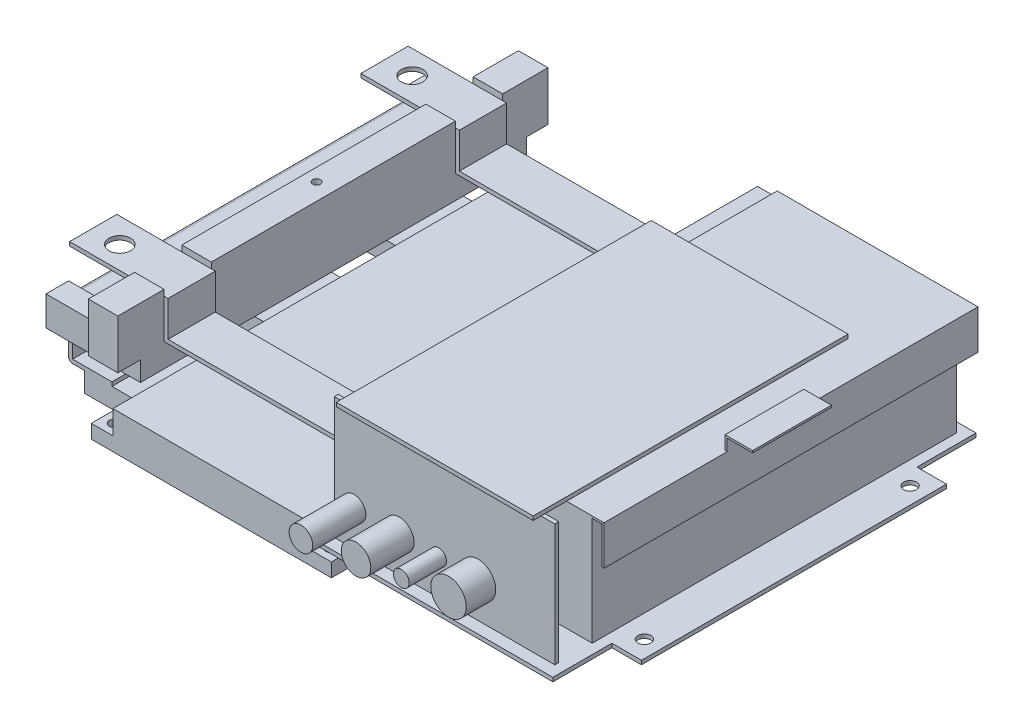
SolidWorks part; units mm, degrees
ref_plane "Płaszczyzna przednia" through (0, 0, 0) normal (0, 0, 1) x (1, 0, 0)
ref_plane "Płaszczyzna górna" through (0, 0, 0) normal (0, 1, 0) x (1, 0, 0)
ref_plane "Płaszczyzna prawa" through (0, 0, 0) normal (1, 0, 0) x (0, 0, -1)
sketch "Szkic1" plane through (0, 0, 0) normal (0, 1, 0) x (1, 0, 0)
  line L1 (-61, -31) -> (61, -31)
  line L2 (-61, -31) -> (-61, 31)
  line L3 (-61, 31) -> (61, 31)
  line L4 (61, -31) -> (61, 31)
  line L5 (-61, -31) -> (61, 31) construction
  line L6 (-61, 31) -> (61, -31) construction
  line L7 (-61, 36) -> (61, 36)
  line L8 (-61, 36) -> (-61, 98)
  line L9 (-61, 98) -> (61, 98)
  line L10 (61, 36) -> (61, 98)
  line L11 (-61, 36) -> (61, 98) construction
  line L12 (-61, 98) -> (61, 36) construction
  line L13 (-61, -98) -> (61, -98)
  line L14 (-61, -98) -> (-61, -36)
  line L15 (-61, -36) -> (61, -36)
  line L16 (61, -98) -> (61, -36)
  line L17 (-61, -98) -> (61, -36) construction
  line L18 (-61, -36) -> (61, -98) construction
  point P0 (0, 0)
  point P6 (0, 67)
  point P11 (0, -67)
  dimension "D1" = 122
  dimension "D2" = 62
  dimension "D3" = 5
  dimension "D4" = 5
extrude "Dodanie-wyciągnięcie1" add sketch "Szkic1" along normal blind 7
sketch "Szkic2" plane through (0, 7, 0) normal (0, 1, 0) x (1, 0, 0)
  line L0 (61, -36) -> (-61, -36) construction
  line L1 (50, -36) -> (-50, -36)
  line L2 (50, -36) -> (50, -98)
  line L3 (50, -98) -> (-50, -98)
  line L4 (-50, -36) -> (-50, -98)
  line L5 (-61, -98) -> (61, -98) construction
  line L6 (-61, -31) -> (61, -31) construction
  line L7 (50, -31) -> (-50, -31)
  line L8 (50, -31) -> (50, 31)
  line L9 (50, 31) -> (-50, 31)
  line L10 (-50, -31) -> (-50, 31)
  line L11 (61, 31) -> (-61, 31) construction
  line L12 (-61, 36) -> (61, 36) construction
  line L13 (50, 36) -> (-50, 36)
  line L14 (50, 36) -> (50, 98)
  line L15 (50, 98) -> (-50, 98)
  line L16 (-50, 36) -> (-50, 98)
  line L17 (61, 98) -> (-61, 98) construction
  line L18 (61, -98) -> (61, -36) construction
  dimension "D1" = 100
  dimension "D2" = 11
extrude "Dodanie-wyciągnięcie2" add sketch "Szkic2" along normal blind 10
sketch "Szkic3" plane through (0, 17, 0) normal (0, 1, 0) x (1, 0, 0)
  line L1 (-50, 98) -> (50, 98)
  line L2 (-50, 98) -> (-50, -98)
  line L3 (-50, -98) -> (50, -98)
  line L4 (50, 98) -> (50, -98)
extrude "Dodanie-wyciągnięcie3" add sketch "Szkic3" along normal blind 2
sketch "Szkic4" plane through (0, 0, 0) normal (0, -1, 0) x (-1, 0, 0)
  line L0 (61, 98) -> (61, 36) construction
  line L1 (-55, -92) -> (55, -92)
  line L2 (-55, -92) -> (-55, -42)
  line L3 (-55, -42) -> (55, -42)
  line L4 (55, -92) -> (55, -42)
  line L5 (-55, -25) -> (55, -25)
  line L6 (-55, -25) -> (-55, 25)
  line L7 (-55, 25) -> (55, 25)
  line L8 (55, -25) -> (55, 25)
  line L9 (-55, 42) -> (55, 42)
  line L10 (-55, 42) -> (-55, 92)
  line L11 (-55, 92) -> (55, 92)
  line L12 (55, 42) -> (55, 92)
  line L13 (-61, 98) -> (61, 98) construction
  dimension "D1" = 50
  dimension "D2" = 110
  dimension "D3" = 6
  dimension "D4" = 6
  dimension "D5" = 17
  dimension "D6" = 17
hole_wizard "Otwór pod śrubę M51" positions "Szkic 3D1" profile "Szkic5" hole size "M5" standard "ISO"
sketch3d "Szkic 3D1"
  point P0 (55, 0, 92)
  point P3 (55, 0, 42)
  point P6 (55, 0, 25)
  point P9 (55, 0, -25)
  point P12 (55, 0, -42)
  point P15 (55, 0, -92)
  point P18 (-55, 0, -92)
  point P21 (-55, 0, -42)
  point P24 (-55, 0, -25)
  point P27 (-55, 0, 25)
  point P30 (-55, 0, 42)
  point P33 (-55, 0, 92)
sketch "Szkic5" plane through (55, 0, 92) normal (1, 0, 0) x (0, 0, -1)
  line L0 (0, 0) -> (0, 15.6524)
  line L1 (0, 15.6524) -> (2.75, 14)
  line L2 (2.75, 14) -> (2.75, 0)
  line L5 (2.75, 0) -> (0, 0)
  line L10 (0, 15.6524) -> (-2.75, 14) construction
  line L11 (0, -6.35) -> (0, 107.95) construction
  dimension "Średnica otworu" = 5.5
  dimension "Głębokość otworu" = 14
  dimension "Kąt wiertła" = 118
sketch "Szkic6" plane through (0, 7, 0) normal (0, 1, 0) x (1, 0, 0)
  line L0 (61, 36) -> (61, 98) construction
  line L1 (61, 86.5) -> (50, 86.5)
  line L2 (61, 86.5) -> (61, 47.5)
  line L3 (61, 47.5) -> (50, 47.5)
  line L4 (50, 86.5) -> (50, 47.5)
  line L5 (50, 36) -> (50, 98) construction
  line L6 (61, -31) -> (61, 31) construction
  line L7 (61, 19.5) -> (50, 19.5)
  line L8 (61, 19.5) -> (61, -19.5)
  line L9 (61, -19.5) -> (50, -19.5)
  line L10 (50, 19.5) -> (50, -19.5)
  line L11 (50, -31) -> (50, 31) construction
  line L12 (61, -98) -> (61, -36) construction
  line L13 (61, -47.5) -> (50, -47.5)
  line L14 (61, -47.5) -> (61, -86.5)
  line L15 (61, -86.5) -> (50, -86.5)
  line L16 (50, -47.5) -> (50, -86.5)
  line L17 (50, -98) -> (50, -36) construction
  line L18 (-50, -36) -> (-50, -98) construction
  line L19 (-50, -47.5) -> (-61, -47.5)
  line L20 (-50, -47.5) -> (-50, -86.5)
  line L21 (-50, -86.5) -> (-61, -86.5)
  line L22 (-61, -47.5) -> (-61, -86.5)
  line L23 (-61, -36) -> (-61, -98) construction
  line L24 (-50, 31) -> (-50, -31) construction
  line L25 (-50, 19.5) -> (-61, 19.5)
  line L26 (-50, 19.5) -> (-50, -19.5)
  line L27 (-50, -19.5) -> (-61, -19.5)
  line L28 (-61, 19.5) -> (-61, -19.5)
  line L29 (-61, 31) -> (-61, -31) construction
  line L30 (-50, 98) -> (-50, 36) construction
  line L31 (-50, 86.5) -> (-61, 86.5)
  line L32 (-50, 86.5) -> (-50, 47.5)
  line L33 (-50, 47.5) -> (-61, 47.5)
  line L34 (-61, 86.5) -> (-61, 47.5)
  line L35 (-61, 98) -> (-61, 36) construction
  line L36 (-61, -98) -> (-50, -98) construction
  line L38 (-61, -31) -> (-50, -31) construction
  line L39 (-61, 36) -> (-50, 36) construction
  line L40 (61, 86.5) -> (76, 86.5)
  line L41 (-61, -86.5) -> (-76, -86.5)
  line L42 (-61, -86.5) -> (-61, -47.5)
  line L43 (-61, -47.5) -> (-76, -47.5)
  line L44 (-76, -86.5) -> (-76, -47.5)
  line L45 (-61, -19.5) -> (-76, -19.5)
  line L46 (-61, -19.5) -> (-61, 19.5)
  line L47 (-61, 19.5) -> (-76, 19.5)
  line L48 (-76, -19.5) -> (-76, 19.5)
  line L49 (-61, 47.5) -> (-76, 47.5)
  line L50 (-61, 47.5) -> (-61, 86.5)
  line L51 (-61, 86.5) -> (-76, 86.5)
  line L52 (-76, 47.5) -> (-76, 86.5)
  line L53 (61, 86.5) -> (61, 47.5)
  line L54 (61, 47.5) -> (76, 47.5)
  line L55 (76, 86.5) -> (76, 47.5)
  line L56 (61, 19.5) -> (76, 19.5)
  line L57 (61, 19.5) -> (61, -19.5)
  line L58 (61, -19.5) -> (76, -19.5)
  line L59 (76, 19.5) -> (76, -19.5)
  line L60 (61, -47.5) -> (76, -47.5)
  line L61 (61, -47.5) -> (61, -86.5)
  line L62 (61, -86.5) -> (76, -86.5)
  line L63 (76, -47.5) -> (76, -86.5)
  line M51 (50, 98) -> (50, 36)
  line M53 (61, 36) -> (61, 98)
  dimension "D1" = 39
  dimension "D2" = 11.5
  dimension "D3" = 11.5
  dimension "D4" = 11.5
  dimension "D5" = 15
extrude "Dodanie-wyciągnięcie4" add sketch "Szkic6" along normal blind 10 contours L44 L41 L22 L43 | L19 L22 L21 L20 | L48 L45 L28 L47 | L25 L28 L27 L26 | L31 L34 L33 L32 | L52 L49 L34 L51 | L3 L1 M53 M51 | L55 L40 L54 M53 | L7 L10 L9 L8 | L59 L56 L8 L58 | L13 L16 L15 L14 | L63 L60 L14 L62
sketch "Szkic7" plane through (0, 0, 86.5) normal (0, 0, 1) x (1, 0, 0)
  line L0 (-62, 17) -> (-62, 19)
  line L1 (-50, 17) -> (-76, 17) construction
  line L2 (-62, 19) -> (-82, 19)
  line L3 (-82, 19) -> (-82, 45.4547)
  line L4 (-82, 45.4547) -> (-51, 45.4547)
  line L5 (-51, 45.4547) -> (-51, 47.4547)
  line L6 (-51, 47.4547) -> (-84, 47.4547)
  line L7 (-84, 47.4547) -> (-84, 17)
  line L8 (-84, 17) -> (-62, 17)
  line L10 (-50, 19) -> (-50, 7) construction
  dimension "D1" = 2
  dimension "D2" = 2
  dimension "D3" = 2
  dimension "D4" = 12
  dimension "D5" = 22
  dimension "D6" = 33
extrude "Dodanie-wyciągnięcie5" add sketch "Szkic7" against normal up to surface (173 mm away) up to face at (-62.6, 11, -86.5)
fillet "Zaokrąglenie1" radius 2 2 edges at (-84, 47.4547, 0) (-84, 17, 0)
sketch "Szkic8" plane through (0, 47.4547, 0) normal (0, 1, 0) x (1, 0, 0)
  line L0 (-69, 37) -> (-69, -37)
  line L1 (-82, 86.5) -> (-51, 86.5) construction
  line L4 (-84, -86.5) -> (-84, 86.5) construction
  point P4 (-69, 0)
  dimension "D1" = 49.5
  dimension "D2" = 37
  dimension "D3" = 15
hole_wizard "Otwór gwintowany M101" positions "Szkic 3D2" profile "Szkic9" tap size "M10" standard "ISO"
sketch3d "Szkic 3D2"
  point P0 (-69, 47.4547, -37)
  point P3 (-69, 47.4547, 0)
  point P6 (-69, 47.4547, 37)
cosmetic thread "Gwint otworu1" parameters "D2"=10
cosmetic thread "Gwint otworu2" parameters "D2"=10
cosmetic thread "Gwint otworu3" parameters "D2"=10
sketch "Szkic9" plane through (-69, 47.4547, -37) normal (1, 0, 0) x (0, 0, 1)
  line L0 (0, 0) -> (0, 2)
  line L1 (0, 2) -> (4.25, 2)
  line L2 (4.25, 2) -> (4.25, 0)
  line L5 (4.25, 0) -> (0, 0)
  line L11 (0, -6.35) -> (0, 107.95) construction
  dimension "Średnica otworu gwintowanego na wylot" = 8.5
  dimension "Głębokość otworu gwintowanego na wylot" = 2
sketch "Szkic11" plane through (-84, 0, 0) normal (-1, 0, 0) x (0, 0, 1)
  line L0 (86.5, 45.4547) -> (86.5, 19) construction
  line L1 (86.5, 37.4547) -> (98, 37.4547)
  line L2 (86.5, 37.4547) -> (86.5, 52.4547)
  line L3 (86.5, 52.4547) -> (98, 52.4547)
  line L4 (98, 37.4547) -> (98, 52.4547)
  line L5 (-86.5, 19) -> (-86.5, 45.4547) construction
  line L6 (-86.5, 37.4547) -> (-98, 37.4547)
  line L7 (-86.5, 37.4547) -> (-86.5, 52.4547)
  line L8 (-86.5, 52.4547) -> (-98, 52.4547)
  line L9 (-98, 37.4547) -> (-98, 52.4547)
  line L12 (-86.5, 47.4547) -> (86.5, 47.4547) construction
  dimension "D1" = 11.5
  dimension "D2" = 11.5
  dimension "D3" = 15
  dimension "D4" = 5
extrude "Dodanie-wyciągnięcie7" add sketch "Szkic11" against normal blind 48
sketch "Szkic12" plane through (0, 0, 86.5) normal (0, 0, -1) x (-1, 0, 0)
  line L0 (82, 45.4547) -> (82, 37.4547)
  line L1 (82, 37.4547) -> (36, 37.4547)
  line L2 (36, 37.4547) -> (82, 37.4547) construction
  line L3 (36, 37.4547) -> (36, 72.4547)
  line L4 (36, 72.4547) -> (51, 72.4547)
  line L5 (51, 72.4547) -> (51, 45.4547)
  line L6 (51, 45.4547) -> (82, 45.4547)
  dimension "D1" = 15
  dimension "D2" = 35
extrude "Dodanie-wyciągnięcie8" add sketch "Szkic12" along normal up to surface and the other way up to surface up to face at (-60, 44.9547, -98) other way up to face at (-60, 44.9547, 98)
sketch "Szkic13" plane through (0, 0, 98) normal (0, 0, 1) x (1, 0, 0)
  line L1 (-36, 72.4547) -> (-51, 72.4547)
  line L2 (-36, 72.4547) -> (-36, 47.4547)
  line L3 (-36, 47.4547) -> (-51, 47.4547)
  line L4 (-51, 72.4547) -> (-51, 47.4547)
  dimension "D1" = 25
  dimension "D2" = 15
extrude "Dodanie-wyciągnięcie9" add sketch "Szkic13" along normal blind 11.5
sketch "Szkic14" plane through (0, 0, -98) normal (0, 0, -1) x (-1, 0, 0)
  line L0 (36, 72.4547) -> (36, 37.4547) construction
  line L1 (51, 72.4547) -> (36, 72.4547)
  line L2 (51, 72.4547) -> (51, 47.4547)
  line L3 (51, 47.4547) -> (36, 47.4547)
  line L4 (36, 72.4547) -> (36, 47.4547)
  dimension "D1" = 25
extrude "Dodanie-wyciągnięcie10" add sketch "Szkic14" along normal blind 11
sketch "Szkic15" plane through (0, 72.4547, 0) normal (0, 1, 0) x (1, 0, 0)
  line L0 (-51, 109) -> (-51, -109.5) construction
  line L1 (-51, 86) -> (-36, 86)
  line L2 (-51, 86) -> (-51, 62)
  line L3 (-51, 62) -> (-36, 62)
  line L4 (-36, 86) -> (-36, 62)
  line L5 (-36, 109) -> (-36, -109.5) construction
  line L7 (-36, -62) -> (-51, -62)
  line L8 (-36, -62) -> (-36, -86)
  line L9 (-36, -86) -> (-51, -86)
  line L10 (-51, -62) -> (-51, -86)
  dimension "D1" = 24
  dimension "D2" = 124
  dimension "D3" = 62
extrude "Wytnij-wyciągnięcie1" cut sketch "Szkic15" against normal blind 5
sketch "Szkic16" plane through (0, 17, 0) normal (0, 1, 0) x (1, 0, 0)
  line L1 (76, -49.5) -> (60, -49.5)
  line L2 (76, -49.5) -> (76, -84.5)
  line L3 (76, -84.5) -> (60, -84.5)
  line L4 (60, -49.5) -> (60, -84.5)
  line L5 (76, 17.5) -> (60, 17.5)
  line L6 (76, 17.5) -> (76, -17.5)
  line L7 (76, -17.5) -> (60, -17.5)
  line L8 (60, 17.5) -> (60, -17.5)
  line L9 (76, 84.5) -> (60, 84.5)
  line L10 (76, 84.5) -> (76, 49.5)
  line L11 (76, 49.5) -> (60, 49.5)
  line L12 (60, 84.5) -> (60, 49.5)
  line L14 (76, 86.5) -> (76, 47.5) construction
  line L15 (76, -86.5) -> (50, -86.5) construction
  line L17 (76, -19.5) -> (50, -19.5) construction
  line L18 (76, 86.5) -> (50, 86.5) construction
  dimension "D1" = 16
  dimension "D2" = 35
  dimension "D3" = 2
  dimension "D4" = 2
  dimension "D5" = 2
extrude "Dodanie-wyciągnięcie11" add sketch "Szkic16" along normal blind 3
sketch "Szkic17" plane through (0, 20, 0) normal (0, 1, 0) x (1, 0, 0)
  line L1 (60, 107.5) -> (183, 107.5)
  line L2 (60, 107.5) -> (60, -107.5)
  line L3 (60, -107.5) -> (183, -107.5)
  line L4 (183, 107.5) -> (183, -107.5)
  line L5 (183, 77.5) -> (198, 77.5)
  line L6 (183, 77.5) -> (183, -77.5)
  line L7 (183, -77.5) -> (198, -77.5)
  line L8 (198, 77.5) -> (198, -77.5)
  line M7 (76, -84.5) -> (76, -49.5)
  line M8 (76, -49.5) -> (60, -49.5)
  line M9 (60, -49.5) -> (60, -84.5)
  line M10 (60, -84.5) -> (76, -84.5)
  dimension "D1" = 123
  dimension "D2" = 215
  dimension "D3" = 107.5
  dimension "D4" = 30
  dimension "D5" = 30
  dimension "D6" = 15
extrude "Dodanie-wyciągnięcie14" add sketch "Szkic17" along normal blind 2 contours L4 L1 L2 L3 M8 M7 M10 | M10 M7 M8 M9 | L8 L5 L4 L7
sketch "Szkic18" plane through (0, 22, 0) normal (0, 1, 0) x (1, 0, 0)
  line L0 (189.5, 67.5) -> (189.5, -67.5) construction
  line L1 (198, 77.5) -> (198, -77.5) construction
  line L2 (183, 77.5) -> (198, 77.5) construction
  line L3 (183, -77.5) -> (198, -77.5) construction
  dimension "D1" = 8.5
  dimension "D2" = 10
  dimension "D3" = 10
hole_wizard "Otwór pod śrubę M61" positions "Szkic 3D3" profile "Szkic19" hole size "M6" standard "ISO" end condition up to next
sketch3d "Szkic 3D3"
  point P0 (189.5, 22, -67.5)
  point P3 (189.5, 22, 67.5)
sketch "Szkic19" plane through (189.5, 22, -67.5) normal (1, 0, 0) x (0, 0, 1)
  line L0 (0, 0) -> (0, 2)
  line L1 (0, 2) -> (3.3, 2)
  line L2 (3.3, 2) -> (3.3, 0)
  line L5 (3.3, 0) -> (0, 0)
  line L11 (0, -6.35) -> (0, 107.95) construction
  dimension "Średnica otworu na wylot" = 6.6
  dimension "Głębokość otworu na wylot" = 2
sketch "Szkic20" plane through (0, 45.4547, 0) normal (0, 1, 0) x (1, 0, 0)
  circle A0 centre (-69, 37) radius 5
  circle A1 centre (-69, 0) radius 5
  circle A2 centre (-69, -37) radius 5
  dimension "D1" = 10
extrude "Wytnij-wyciągnięcie2" cut sketch "Szkic20" against normal up to surface (8 mm away) up to face at (-71.5, 37.4547, 0)
sketch "Szkic21" plane through (0, 22, 0) normal (0, 1, 0) x (1, 0, 0)
  line L0 (60, 107.5) -> (183, 107.5) construction
  line L1 (178, 102.5) -> (83, 102.5)
  line L2 (178, 102.5) -> (178, -82.5)
  line L3 (178, -82.5) -> (83, -82.5)
  line L4 (83, 102.5) -> (83, -82.5)
  line L5 (183, 107.5) -> (183, 77.5) construction
  dimension "D1" = 95
  dimension "D2" = 185
  dimension "D3" = 5
  dimension "D4" = 5
extrude "Dodanie-wyciągnięcie15" add sketch "Szkic21" along normal blind 55 separate body
sketch "Szkic22" plane through (0, 0, 62) normal (0, 0, 1) x (1, 0, 0)
  line L0 (-51, 67.4547) -> (-84, 67.4547)
  line L1 (-84, 67.4547) -> (-84, 69.4547)
  line L2 (-84, 69.4547) -> (-34, 69.4547)
  line L3 (-34, 69.4547) -> (-34, 51.4547)
  line L4 (-34, 51.4547) -> (56, 51.4547)
  line L5 (56, 51.4547) -> (56, 27)
  line L6 (56, 27) -> (76, 27)
  line L7 (76, 27) -> (76, 25)
  line L8 (76, 25) -> (54, 25)
  line L9 (54, 25) -> (54, 49.4547)
  line L10 (54, 49.4547) -> (-36, 49.4547)
  line L11 (-36, 49.4547) -> (-36, 67.4547)
  line L12 (-36, 67.4547) -> (-51, 67.4547)
  line L13 (60, 22) -> (183, 22) construction
  line L14 (76, 17) -> (76, 7) construction
  dimension "D1" = 2
  dimension "D2" = 2
  dimension "D3" = 2
  dimension "D4" = 2
  dimension "D5" = 2
  dimension "D6" = 22
  dimension "D7" = 33
  dimension "D8" = 2
  dimension "D9" = 18
  dimension "D10" = 3
extrude "Dodanie-wyciągnięcie16" add sketch "Szkic22" along normal up to surface (24 mm away) separate body up to face at (-43.5, 69.9547, 86)
mirror "Lustro3" about plane through (0, 0, 0) normal (0, 0, 1) of bodies 123
sketch "Szkic23" plane through (0, 69.4547, 0) normal (0, 1, 0) x (1, 0, 0)
  line L0 (-70, 74) -> (-70, -74.5)
  line L1 (-84, 86) -> (-84, 62) construction
  line L2 (-34, 86) -> (-84, 86) construction
  line L3 (-51, -86.5) -> (-82, -86.5) construction
  dimension "D1" = 14
  dimension "D2" = 12
  dimension "D3" = 12
hole_wizard "Otwór pod śrubę M101" positions "Szkic 3D5" profile "Szkic24" hole size "M10" standard "ISO"
sketch3d "Szkic 3D5"
  point P0 (-70, 69.4547, -74)
  point P3 (-70, 69.4547, 74.5)
sketch "Szkic24" plane through (-70, 69.4547, -74) normal (1, 0, 0) x (0, 0, 1)
  line L0 (0, 0) -> (0, 32)
  line L1 (0, 32) -> (5.5, 32)
  line L2 (5.5, 32) -> (5.5, 0)
  line L5 (5.5, 0) -> (0, 0)
  line L11 (0, -6.35) -> (0, 107.95) construction
  dimension "Średnica otworu na wylot" = 11
  dimension "Głębokość otworu na wylot" = 32
sketch "Szkic25" plane through (0, 0, 82.5) normal (0, 0, 1) x (1, 0, 0)
  line L0 (74, 74) -> (83, 74)
  line L1 (83, 77) -> (83, 22) construction
  line L2 (83, 74) -> (83, 77)
  line L3 (83, 77) -> (183, 77)
  line L4 (183, 77) -> (183, 58)
  line L5 (183, 58) -> (184, 58)
  line L6 (184, 58) -> (184, 78)
  line L7 (184, 78) -> (82, 78)
  line L8 (82, 78) -> (82, 75)
  line L9 (82, 75) -> (72, 75)
  line L10 (72, 75) -> (72, 74)
  line L11 (72, 74) -> (74, 74)
  line L12 (178, 77) -> (178, 22) construction
  dimension "D1" = 1
  dimension "D2" = 1
  dimension "D3" = 1
  dimension "D4" = 1
  dimension "D5" = 3
  dimension "D6" = 10
  dimension "D7" = 9
  dimension "D8" = 3
  dimension "D9" = 20
  dimension "D10" = 5
extrude "Dodanie-wyciągnięcie17" add sketch "Szkic25" against normal blind 190
sketch "Szkic26" plane through (0, 22, 0) normal (0, 1, 0) x (1, 0, 0)
  line L0 (60, -107.5) -> (183, -107.5) construction
  line L1 (66, -99.5) -> (178, -99.5)
  line L2 (66, -99.5) -> (66, -101.5)
  line L3 (66, -101.5) -> (178, -101.5)
  line L4 (178, -99.5) -> (178, -101.5)
  line L5 (60, 107.5) -> (60, -107.5) construction
  dimension "D1" = 6
  dimension "D2" = 2
  dimension "D3" = 112
  dimension "D4" = 6
extrude "Dodanie-wyciągnięcie18" add sketch "Szkic26" along normal blind 62
sketch "Szkic27" plane through (0, 84, 0) normal (0, 1, 0) x (1, 0, 0)
  line L0 (66, -99.5) -> (66, -101.5) construction
  line L1 (71, -105.5) -> (171, -105.5)
  line L2 (71, -105.5) -> (71, 54.5)
  line L3 (71, 54.5) -> (171, 54.5)
  line L4 (171, -105.5) -> (171, 54.5)
  line L5 (66, -101.5) -> (178, -101.5) construction
  dimension "D1" = 100
  dimension "D2" = 160
  dimension "D3" = 5
  dimension "D4" = 4
extrude "Dodanie-wyciągnięcie19" add sketch "Szkic27" along normal blind 2
sketch "Szkic28" plane through (0, 84, 0) normal (0, -1, 0) x (-1, 0, 0)
  line L0 (-71, 54.5) -> (-71, -99.5) construction
  line L1 (-71, 54.5) -> (-80, 54.5)
  line L2 (-71, 54.5) -> (-71, -0.5)
  line L3 (-71, -0.5) -> (-80, -0.5)
  line L4 (-80, 54.5) -> (-80, -0.5)
  line L5 (-171, 54.5) -> (-71, 54.5) construction
  dimension "D1" = 55
  dimension "D2" = 9
  dimension "D3" = 55
extrude "Dodanie-wyciągnięcie20" add sketch "Szkic28" along normal up to surface (9 mm away) up to face at (77, 75, -12.5)
sketch "Szkic29" plane through (0, 0, 0) normal (0, 0, 1) x (1, 0, 0)
  line L0 (183, 85) -> (197, 85)
  line L1 (197, 85) -> (197, 84)
  line L2 (197, 84) -> (184, 84)
  line L3 (184, 84) -> (184, 78)
  line L6 (184, 78) -> (82, 78) construction
  line L7 (183, 85) -> (183, 78)
  line L8 (184, 78) -> (183, 78)
  line L9 (183, 77) -> (183, 58) construction
  dimension "D1" = 1
  dimension "D2" = 14
  dimension "D3" = 7
  dimension "D4" = 1
  dimension "D5" = 1
extrude "Dodanie-wyciągnięcie21" add sketch "Szkic29" along normal mid plane 40
sketch "Szkic30" plane through (0, 72.4547, 0) normal (0, 1, 0) x (1, 0, 0)
  line L0 (-51, 62) -> (-51, -62) construction
  line L2 (-44.5, 0) -> (0, 0)
  point P0 (-44.5, 0)
  dimension "D1" = 6.5
hole_wizard "Otwory ustalające Ø4.0mm1" positions "Szkic 3D6" profile "Szkic31" hole size "Ø4.0" standard "ISO"
sketch3d "Szkic 3D6"
  point P0 (-44.5, 72.4547, 0)
sketch "Szkic31" plane through (-44.5, 72.4547, 0) normal (1, 0, 0) x (0, 0, 1)
  line L0 (0, 0) -> (0, 35)
  line L1 (0, 35) -> (2, 35)
  line L2 (2, 35) -> (2, 0)
  line L5 (2, 0) -> (0, 0)
  line L11 (0, -6.35) -> (0, 107.95) construction
  dimension "Średnica otworu na wylot" = 4
  dimension "Głębokość otworu na wylot" = 35
sketch "Szkic32" plane through (0, 0, 101.5) normal (0, 0, 1) x (1, 0, 0)
  line L0 (76, 40) -> (139, 40)
  line L1 (-61, 0) -> (61, 0) construction
  point P2 (99, 40)
  point P3 (119, 40)
  dimension "D1" = 40
  dimension "D2" = 23
  dimension "D3" = 20
  dimension "D4" = 20
  dimension "D5" = 16
sketch "Szkic33" plane through (0, 0, 101.5) normal (0, 0, 1) x (1, 0, 0)
  circle A0 centre (76, 40) radius 6
  dimension "D1" = 12
extrude "Dodanie-wyciągnięcie22" add sketch "Szkic33" along normal blind 27
sketch "Szkic34" plane through (0, 0, 101.5) normal (0, 0, 1) x (1, 0, 0)
  circle A0 centre (99, 40) radius 7.5
  dimension "D1" = 15
extrude "Dodanie-wyciągnięcie23" add sketch "Szkic34" along normal blind 22
sketch "Szkic35" plane through (0, 0, 101.5) normal (0, 0, 1) x (1, 0, 0)
  circle A0 centre (119, 40) radius 4
  dimension "D1" = 8
extrude "Dodanie-wyciągnięcie24" add sketch "Szkic35" along normal blind 19
sketch "Szkic36" plane through (0, 0, 101.5) normal (0, 0, 1) x (1, 0, 0)
  circle A0 centre (139, 40) radius 9
  dimension "D1" = 18
extrude "Dodanie-wyciągnięcie25" add sketch "Szkic36" along normal blind 15
